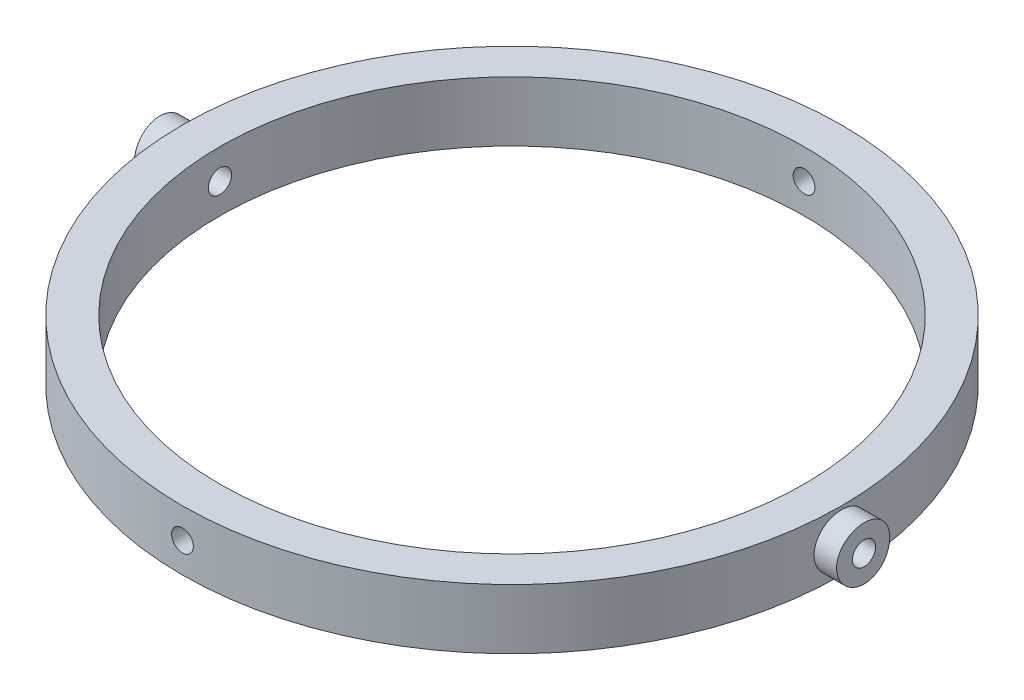
SolidWorks part; units mm, degrees
ref_plane "Front Plane" through (0, 0, 0) normal (0, 0, 1) x (1, 0, 0)
ref_plane "Top Plane" through (0, 0, 0) normal (0, 1, 0) x (1, 0, 0)
ref_plane "Right Plane" through (0, 0, 0) normal (1, 0, 0) x (0, 0, -1)
sketch "Sketch1" plane through (0, 0, 0) normal (0, 1, 0) x (1, 0, 0)
  circle A0 centre (0, 0) radius 39
  circle A1 centre (0, 0) radius 44
  dimension "D1" = 78
  dimension "D2" = 5
extrude "Boss-Extrude1" add sketch "Sketch1" along normal blind 8
sketch "Sketch2" plane through (0, 0, 0) normal (0, 0, 1) x (1, 0, 0)
  line L0 (0, 0) -> (0, 8) construction
  line L1 (44, 8) -> (-44, 8) construction
  circle A0 centre (0, 4) radius 1.45
  dimension "D1" = 2.9
extrude "Cut-Extrude1" cut sketch "Sketch2" against normal through all both and the other way through all
sketch "Sketch3" plane through (0, 0, 0) normal (1, 0, 0) x (0, 0, -1)
  line L0 (0, 0) -> (0, 8) construction
  line L1 (39, 8) -> (-39, 8) construction
  circle A0 centre (0, 4) radius 1.55
  dimension "D1" = 3.1
extrude "Cut-Extrude2" cut sketch "Sketch3" against normal through all both and the other way through all
ref_plane "Plane1" through (47, 0, 0) normal (1, 0, 0) x (0, 0, -1)
sketch "Sketch4" plane through (47, 0, 0) normal (1, 0, 0) x (0, 0, -1)
  line L0 (0, 0) -> (0, 8) construction
  line L1 (44, 8) -> (-44, 8) construction
  circle A0 centre (0, 4) radius 1.55
  circle A1 centre (0, 4) radius 1.55 construction
  circle A2 centre (0, 4) radius 3.55
  dimension "D1" = 2
extrude "Boss-Extrude2" add sketch "Sketch4" against normal up to surface (3.0273 mm away)
mirror "Mirror1" about plane through (0, 0, 0) normal (1, 0, 0) of "Boss-Extrude2"
sketch "Sketch7" plane through (0, 8, 0) normal (0, 1, 0) x (1, 0, 0)
  line L0 (47, -3.55) -> (47, 3.55) construction
  circle A0 centre (0, 0) radius 47
  circle A1 centre (0, 0) radius 50
  dimension "D1" = 3
extrude "Cut-Extrude3" cut sketch "Sketch7" against normal through all
